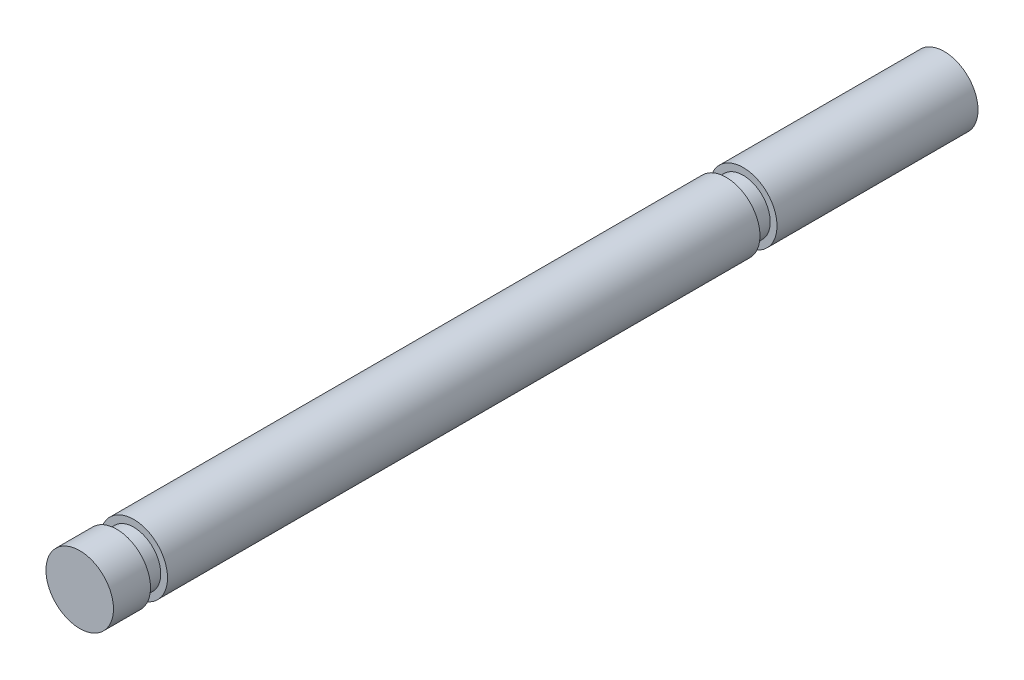
SolidWorks part; units mm, degrees
ref_plane "Front Plane" through (0, 0, 0) normal (0, 0, 1) x (1, 0, 0)
ref_plane "Top Plane" through (0, 0, 0) normal (0, 1, 0) x (1, 0, 0)
ref_plane "Right Plane" through (0, 0, 0) normal (1, 0, 0) x (0, 0, -1)
sketch "Sketch2" plane through (0, 0, 0) normal (0, 0, 1) x (1, 0, 0)
  circle A0 centre (0, 0) radius 3.175
  dimension "D1" = 6.35
extrude "Boss-Extrude1" add sketch "Sketch2" along normal blind 81.28
ref_plane "Plane1" through (0, 0, 20.4978) normal (0, 0, -1) x (-1, 0, 0)
sketch "Sketch3" plane through (0, 0, 20.4978) normal (0, 0, -1) x (-1, 0, 0)
  circle A0 centre (0, 0) radius 2.54
  dimension "D1" = 5.08
extrude "Cut-Extrude1" cut sketch "Sketch3" along normal blind 1.6002 flip side to cut
ref_plane "Plane2" through (0, 0, 76.2) normal (0, 0, 1) x (1, 0, 0)
sketch "Sketch4" plane through (0, 0, 76.2) normal (0, 0, 1) x (1, 0, 0)
  circle A0 centre (0, 0) radius 2.54
  dimension "D1" = 5.08
extrude "Cut-Extrude2" cut sketch "Sketch4" along normal blind 1.6002 flip side to cut
